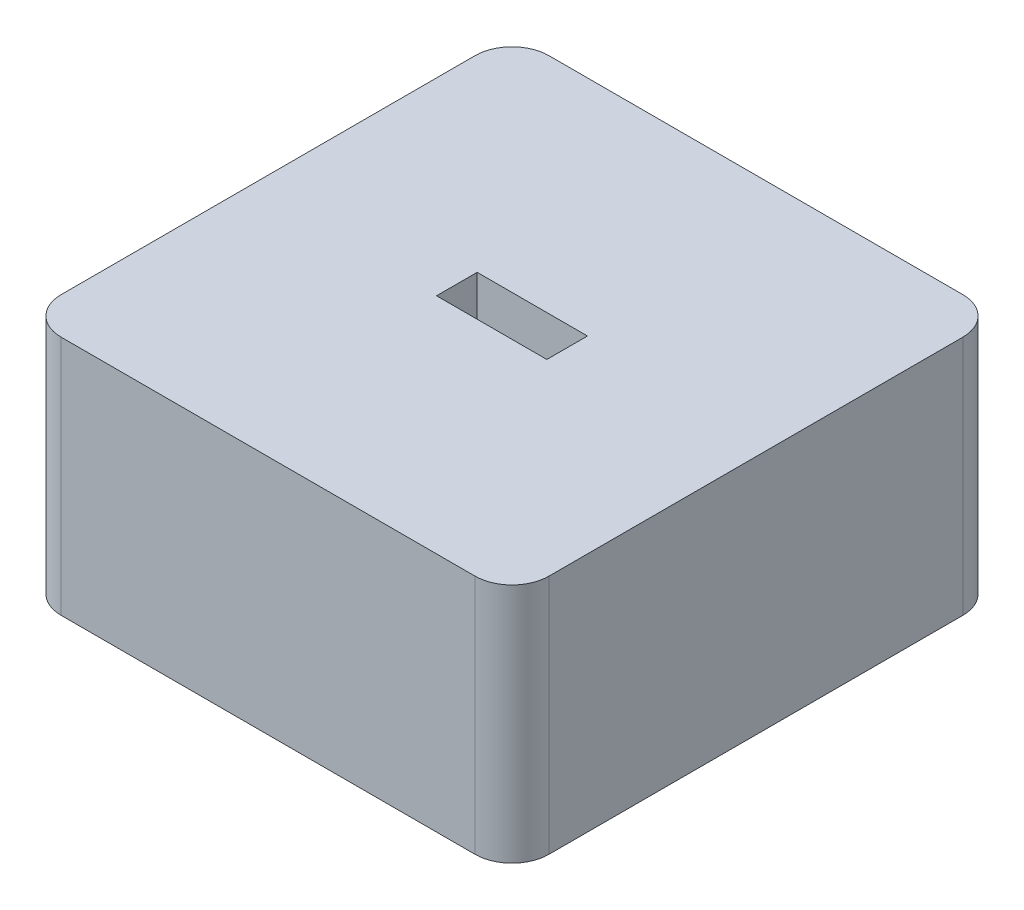
SolidWorks part; units mm, degrees
ref_plane "Front Plane" through (0, 0, 0) normal (0, 0, 1) x (1, 0, 0)
ref_plane "Top Plane" through (0, 0, 0) normal (0, 1, 0) x (1, 0, 0)
ref_plane "Right Plane" through (0, 0, 0) normal (1, 0, 0) x (0, 0, -1)
sketch "Sketch1" plane through (0, 0, 0) normal (0, 1, 0) x (1, 0, 0)
  line L1 (0, 0) -> (42, 0)
  line L2 (0, 0) -> (0, 42)
  line L3 (0, 42) -> (42, 42)
  line L4 (42, 0) -> (42, 42)
  dimension "D1" = 42
extrude "Boss-Extrude1" add sketch "Sketch1" along normal blind 20.75
sketch "Sketch2" plane through (0, 20.75, 0) normal (0, 1, 0) x (1, 0, 0)
  line L0 (21, 22.75) -> (21, 42) construction
  line L1 (16.25, 22.75) -> (25.75, 22.75)
  line L2 (16.25, 22.75) -> (16.25, 19.25)
  line L3 (16.25, 19.25) -> (25.75, 19.25)
  line L4 (25.75, 22.75) -> (25.75, 19.25)
  line L5 (42, 42) -> (0, 42) construction
  line L6 (25.75, 21) -> (42, 21) construction
  line L7 (42, 0) -> (42, 42) construction
  dimension "D1" = 9.5
  dimension "D2" = 3.5
extrude "Cut-Extrude4" cut sketch "Sketch2" against normal blind 3.52 contours L4 L3 L2 L1
sketch "Sketch3" plane through (0, 0, 0) normal (0, -1, 0) x (1, 0, 0)
  line L0 (21, -15.75) -> (21, 0) construction
  line L1 (13.25, -15.75) -> (28.75, -15.75)
  line L2 (13.25, -15.75) -> (13.25, -26.25)
  line L3 (13.25, -26.25) -> (28.75, -26.25)
  line L4 (28.75, -15.75) -> (28.75, -26.25)
  line L6 (28.75, -21) -> (42, -21) construction
  line L8 (0, 0) -> (42, 0) construction
  line L9 (42, 0) -> (42, -42) construction
  dimension "D1" = 15.5
  dimension "D2" = 10.5
extrude "Cut-Extrude1" cut sketch "Sketch3" against normal blind 15.23
sketch "Sketch4" plane through (0, 17.23, 0) normal (0, 1, 0) x (1, 0, 0)
  line L0 (17.975, 21) -> (24.025, 21) construction
  line L1 (17.975, 22.275) -> (24.025, 22.275)
  line L2 (17.975, 19.725) -> (24.025, 19.725)
  line L3 (21, 21) -> (21, 15.75) construction
  line L5 (24.025, 21) -> (28.75, 21) construction
  line L7 (28.75, 15.75) -> (13.25, 15.75) construction
  line L8 (28.75, 26.25) -> (28.75, 15.75) construction
  arc A0 (17.975, 22.275) -> (17.975, 19.725) centre (17.975, 21) ccw
  arc A1 (24.025, 19.725) -> (24.025, 22.275) centre (24.025, 21) ccw
  point P2 (21, 21)
  dimension "D1" = 2.55
  dimension "D2" = 6.05
extrude "Cut-Extrude2" cut sketch "Sketch4" against normal up to next
sketch "Sketch5" plane through (0, 0, 0) normal (0, -1, 0) x (1, 0, 0)
  line L0 (0, -42) -> (0, 0) construction
  line L1 (4, -4) -> (38, -4)
  line L2 (4, -4) -> (4, -38)
  line L3 (4, -38) -> (38, -38)
  line L4 (38, -4) -> (38, -38)
  line L9 (0, 0) -> (42, 0) construction
  line L10 (28.75, -26.25) -> (28.75, -15.75) construction
  line L11 (13.25, -26.25) -> (28.75, -26.25) construction
  line L12 (13.25, -15.75) -> (13.25, -26.25) construction
  line L13 (28.75, -15.75) -> (13.25, -15.75) construction
  line L14 (28.75, -26.25) -> (28.75, -15.75) construction
  line L15 (13.25, -26.25) -> (28.75, -26.25) construction
  line L16 (13.25, -15.75) -> (13.25, -26.25) construction
  line L17 (28.75, -15.75) -> (13.25, -15.75) construction
  line L18 (31.75, -12.75) -> (10.25, -12.75)
  line L19 (10.25, -12.75) -> (10.25, -29.25)
  line L20 (10.25, -29.25) -> (31.75, -29.25)
  line L21 (31.75, -29.25) -> (31.75, -12.75)
  line L22 (42, 0) -> (42, -42) construction
  dimension "D2" = 4
  dimension "D3" = 4
  dimension "D4" = 4
  dimension "D1" = 3
extrude "Cut-Extrude5" cut sketch "Sketch5" against normal blind 10
fillet "Fillet1" radius 3.175 4 edges at (42, 10.375, -42) (42, 10.375, 0) (0, 10.375, 0) (0, 10.375, -42)
